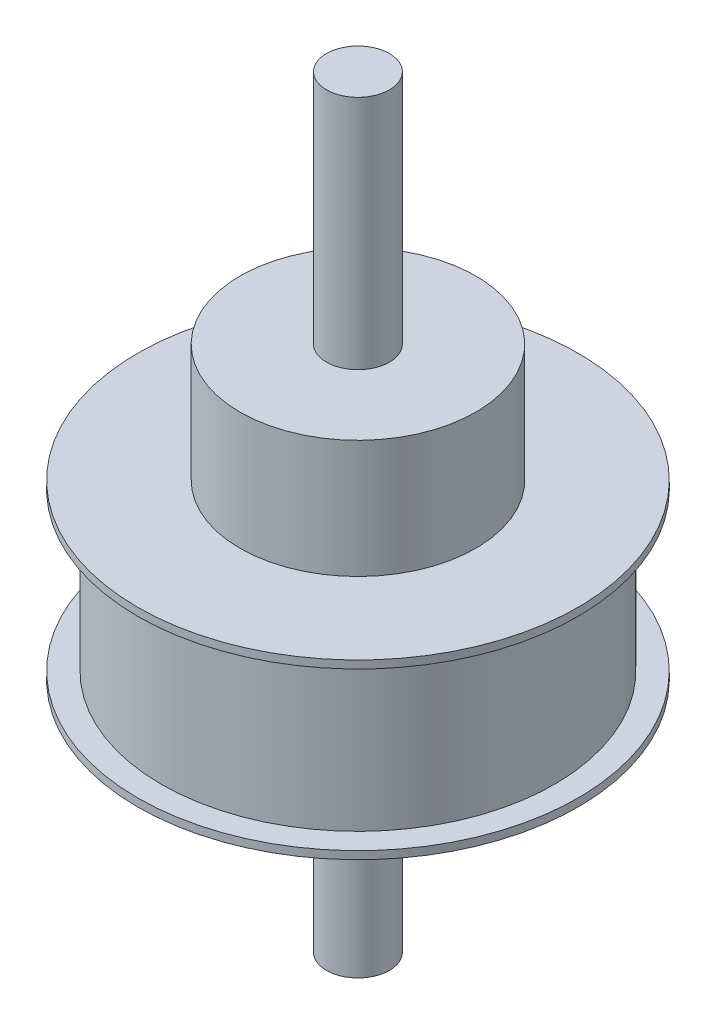
SolidWorks part; units mm, degrees
ref_plane "Front Plane" through (0, 0, 0) normal (0, 0, 1) x (1, 0, 0)
ref_plane "Top Plane" through (0, 0, 0) normal (0, 1, 0) x (1, 0, 0)
ref_plane "Right Plane" through (0, 0, 0) normal (1, 0, 0) x (0, 0, -1)
sketch "Sketch1" plane through (0, 0, 0) normal (0, 1, 0) x (1, 0, 0)
  circle A0 centre (0, 0) radius 25
extrude "Boss-Extrude1" add sketch "Sketch1" along normal blind 21
ref_plane "Plane1" through (0, 0, 0) normal (0, 1, 0) x (1, 0, 0)
sketch "Sketch2" plane through (0, 0, 0) normal (0, 1, 0) x (1, 0, 0)
  circle A0 centre (0, 0) radius 28
extrude "Boss-Extrude2" add sketch "Sketch2" along normal blind 1
ref_plane "Plane2" through (0, 21, 0) normal (0, 1, 0) x (1, 0, 0)
sketch "Sketch3" plane through (0, 21, 0) normal (0, 1, 0) x (1, 0, 0)
  circle A0 centre (0, 0) radius 28
extrude "Boss-Extrude3" add sketch "Sketch3" along normal blind 1
ref_plane "Plane3" through (0, 22, 0) normal (0, 1, 0) x (1, 0, 0)
sketch "Sketch4" plane through (0, 22, 0) normal (0, 1, 0) x (1, 0, 0)
  circle A0 centre (0, 0) radius 15
extrude "Boss-Extrude4" add sketch "Sketch4" along normal blind 15
ref_plane "Plane4" through (0, 37, 0) normal (0, 1, 0) x (1, 0, 0)
sketch "Sketch5" plane through (0, 37, 0) normal (0, 1, 0) x (1, 0, 0)
  circle A0 centre (0, 0) radius 4
extrude "Boss-Extrude5" add sketch "Sketch5" along normal blind 30
ref_plane "Plane5" through (0, 0, 0) normal (0, 1, 0) x (1, 0, 0)
sketch "Sketch6" plane through (0, 0, 0) normal (0, 1, 0) x (1, 0, 0)
  circle A0 centre (0, 0) radius 4
extrude "Boss-Extrude6" add sketch "Sketch6" against normal blind 30
